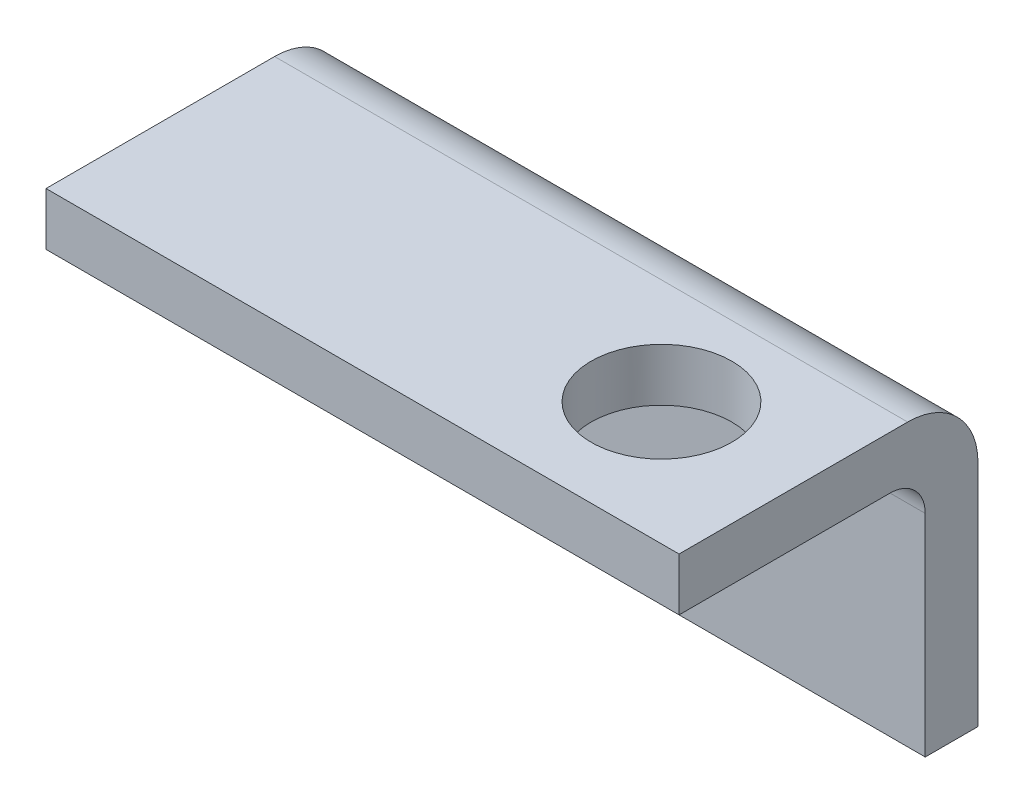
SolidWorks part; units mm, degrees
ref_plane "Płaszczyzna XY" through (0, 0, 0) normal (0, 0, 1) x (1, 0, 0)
ref_plane "Płaszczyzna XZ" through (0, 0, 0) normal (0, 1, 0) x (1, 0, 0)
ref_plane "Płaszczyzna YZ" through (0, 0, 0) normal (1, 0, 0) x (0, 0, -1)
sketch "Sketch1" plane through (0, 0, 0) normal (0, 0, 1) x (1, 0, 0)
  line L1 (-18, 8.5) -> (18, 8.5)
  line L2 (-18, 8.5) -> (-18, -8.5)
  line L3 (-18, -8.5) -> (18, -8.5)
  line L4 (18, 8.5) -> (18, -8.5)
  line L5 (-18, 8.5) -> (18, -8.5) construction
  line L6 (-18, -8.5) -> (18, 8.5) construction
  point P0 (0, 0)
  dimension "D1" = 36
  dimension "D2" = 17
extrude "Boss-Extrude1" add sketch "Sketch1" along normal blind 3
sketch "Sketch15" plane through (0, 0, 3) normal (0, 0, 1) x (1, 0, 0)
  line L0 (-18, 8.5) -> (-18, -8.5) construction
  line L1 (-18, 8.5) -> (-18, 5.5)
  line L2 (18, 8.5) -> (-18, 8.5) construction
  line L3 (18, 8.5) -> (-18, 8.5)
  line L4 (18, -8.5) -> (18, 8.5) construction
  line L5 (18, 5.5) -> (18, 8.5)
  line L6 (-18, 5.5) -> (18, 5.5)
  dimension "D1" = 3
extrude "Boss-Extrude2" add sketch "Sketch15" along normal blind 14
fillet "Fillet2" radius 2 1 edges at (0, 5.5, 3)
fillet "Fillet3" radius 4 1 edges at (0, 8.5, 0)
sketch "Sketch17" plane through (0, -8.5, 0) normal (0, -1, 0) x (1, 0, 0)
  line L0 (-18, 0) -> (18, 0) construction
  line L3 (18, 17) -> (18, 5) construction
  circle A0 centre (10, 10) radius 4
  point P5 (0, 0)
  point P6 (0, 0)
  dimension "D1" = 8
  dimension "D2" = 10
  dimension "D3" = 8
extrude "Cut-Extrude1" cut sketch "Sketch17" against normal through all
sketch "Sketch18" plane through (0, 0, 17) normal (0, 0, 1) x (1, 0, 0)
  line L0 (18, 8.5) -> (-18, 8.5) construction
  line L3 (-18, 3.5) -> (-18, -8.5) construction
  circle A0 centre (-10, -1.5) radius 4
  point P4 (0, 0)
  dimension "D1" = 8
  dimension "D2" = 10
  dimension "D3" = 8
extrude "Cut-Extrude2" cut sketch "Sketch18" against normal through all
